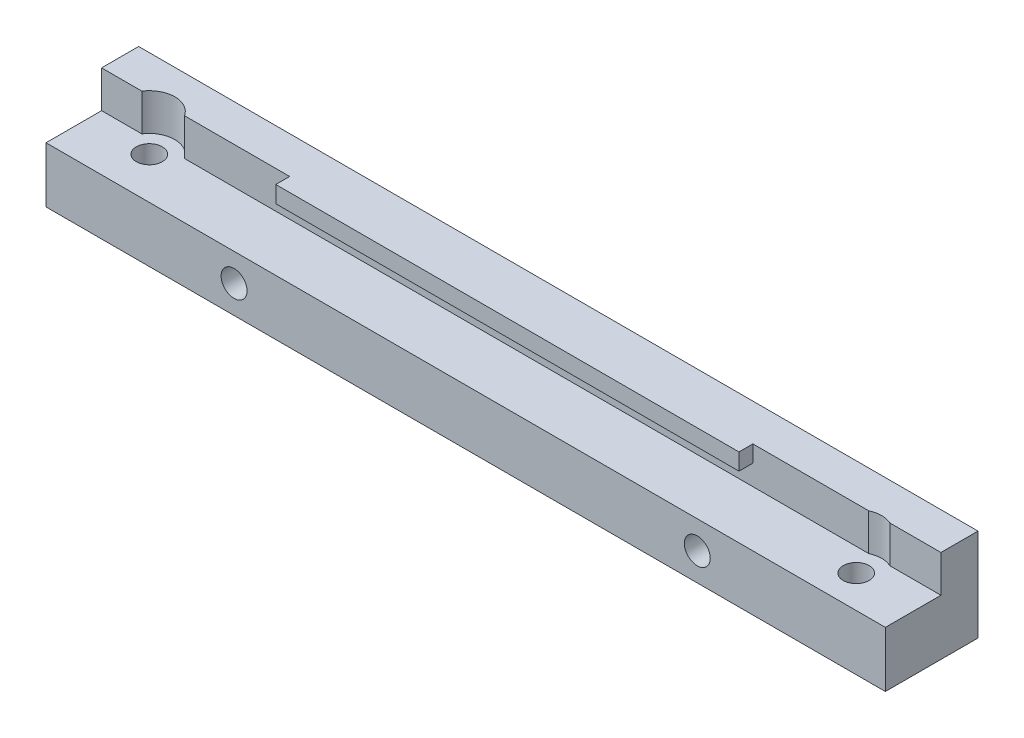
SolidWorks part; units mm, degrees
ref_plane "Plan de face" through (0, 0, 0) normal (0, 0, 1) x (1, 0, 0)
ref_plane "Plan de dessus" through (0, 0, 0) normal (0, 1, 0) x (1, 0, 0)
ref_plane "Plan de droite" through (0, 0, 0) normal (1, 0, 0) x (0, 0, -1)
sketch "Esquisse1" plane through (0, 0, 0) normal (0, 0, 1) x (1, 0, 0)
  line L1 (0, 0) -> (90.6, 0)
  line L2 (0, 0) -> (0, 10)
  line L3 (0, 10) -> (90.6, 10)
  line L4 (90.6, 0) -> (90.6, 10)
  dimension "D1" = 90.6
  dimension "D2" = 10
extrude "Boss.-Extru.1" add sketch "Esquisse1" along normal blind 10
sketch "Esquisse2" plane through (0, 0, 10) normal (0, 0, 1) x (1, 0, 0)
  line L0 (90.6, 0) -> (90.6, 10) construction
  line L1 (0, 10) -> (90.6, 10)
  line L2 (0, 10) -> (0, 6)
  line L3 (0, 6) -> (90.6, 6)
  line L4 (90.6, 10) -> (90.6, 6)
  dimension "D1" = 4
extrude "Enlèv. mat.-Extru.1" cut sketch "Esquisse2" against normal blind 6
sketch "Esquisse3" plane through (0, 6, 0) normal (0, 1, 0) x (1, 0, 0)
  line L0 (0, -4) -> (90.6, -4) construction
  line L1 (0, -4) -> (0, -10) construction
  line L2 (90.6, -4) -> (90.6, -10) construction
  circle A0 centre (6.65, -5.5) radius 1.4
  circle A1 centre (83.95, -6.5) radius 1.4
  dimension "D1" = 2.8
  dimension "D2" = 2.8
  dimension "D3" = 1.5
  dimension "D4" = 2.5
  dimension "D5" = 6.65
  dimension "D6" = 6.65
  dimension "D7" = 77.3
extrude "Enlèv. mat.-Extru.2" cut sketch "Esquisse3" against normal blind 6
sketch "Esquisse4" plane through (0, 0, 4) normal (0, 0, 1) x (1, 0, 0)
  line L0 (90.6, 10) -> (0, 10) construction
  line L1 (20.3, 10) -> (70.3, 10)
  line L2 (20.3, 10) -> (20.3, 8.2)
  line L3 (20.3, 8.2) -> (70.3, 8.2)
  line L4 (70.3, 10) -> (70.3, 8.2)
  line L5 (0, 10) -> (0, 6) construction
  line L6 (90.6, 6) -> (90.6, 10) construction
  dimension "D1" = 1.8
  dimension "D2" = 20.3
  dimension "D3" = 20.3
  dimension "D4" = 50
extrude "Boss.-Extru.2" add sketch "Esquisse4" along normal blind 1.5
sketch "Esquisse5" plane through (0, 10, 0) normal (0, 1, 0) x (1, 0, 0)
  circle A0 centre (6.65, -5.5) radius 2.75
  circle A1 centre (83.95, -6.5) radius 2.75
  dimension "D1" = 5.5
  dimension "D2" = 5.5
extrude "Enlèv. mat.-Extru.3" cut sketch "Esquisse5" against normal blind 4
sketch "Esquisse6" plane through (0, 0, 10) normal (0, 0, 1) x (1, 0, 0)
  line L0 (0, 6) -> (0, 0) construction
  line L1 (90.6, 0) -> (90.6, 6) construction
  line L2 (0, 0) -> (90.6, 0) construction
  circle A0 centre (20.3, 3) radius 1.4
  circle A1 centre (70.3, 3) radius 1.4
  dimension "D1" = 2.8
  dimension "D2" = 2.8
  dimension "D3" = 20.3
  dimension "D4" = 20.3
  dimension "D5" = 50
  dimension "D6" = 3
  dimension "D7" = 3
extrude "Enlèv. mat.-Extru.4" cut sketch "Esquisse6" against normal through all
